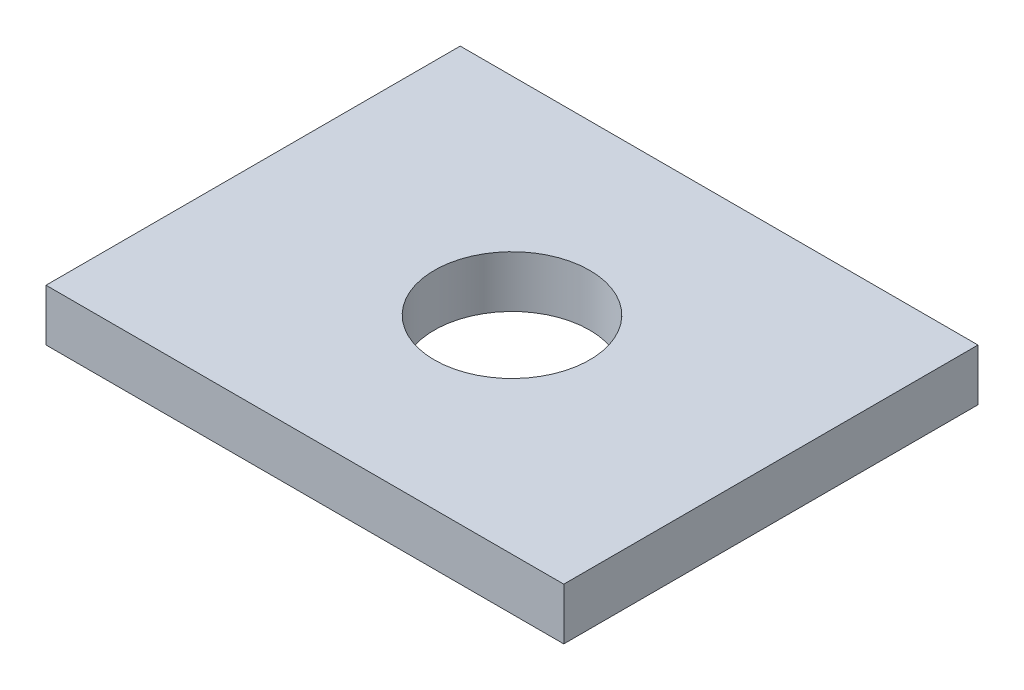
SolidWorks part; units mm, degrees
ref_plane "Front Plane" through (0, 0, 0) normal (0, 0, 1) x (1, 0, 0)
ref_plane "Top Plane" through (0, 0, 0) normal (0, 1, 0) x (1, 0, 0)
ref_plane "Right Plane" through (0, 0, 0) normal (1, 0, 0) x (0, 0, -1)
sketch "Sketch1" plane through (0, 0, 0) normal (0, 1, 0) x (1, 0, 0)
  line L1 (100, 80) -> (-100, 80)
  line L2 (100, 80) -> (100, -80)
  line L3 (100, -80) -> (-100, -80)
  line L4 (-100, 80) -> (-100, -80)
  line L5 (100, 80) -> (-100, -80) construction
  line L6 (100, -80) -> (-100, 80) construction
  point P0 (0, 0)
  dimension "D1" = 200
  dimension "D2" = 160
extrude "base" add sketch "Sketch1" along normal blind 20 contours L1 L4 L3 L2
sketch "Sketch2" plane through (0, 20, 0) normal (0, 1, 0) x (1, 0, 0)
  circle A0 centre (0, 0) radius 30
  dimension "D1" = 60
extrude "actuator cut" cut sketch "Sketch2" against normal blind 40
